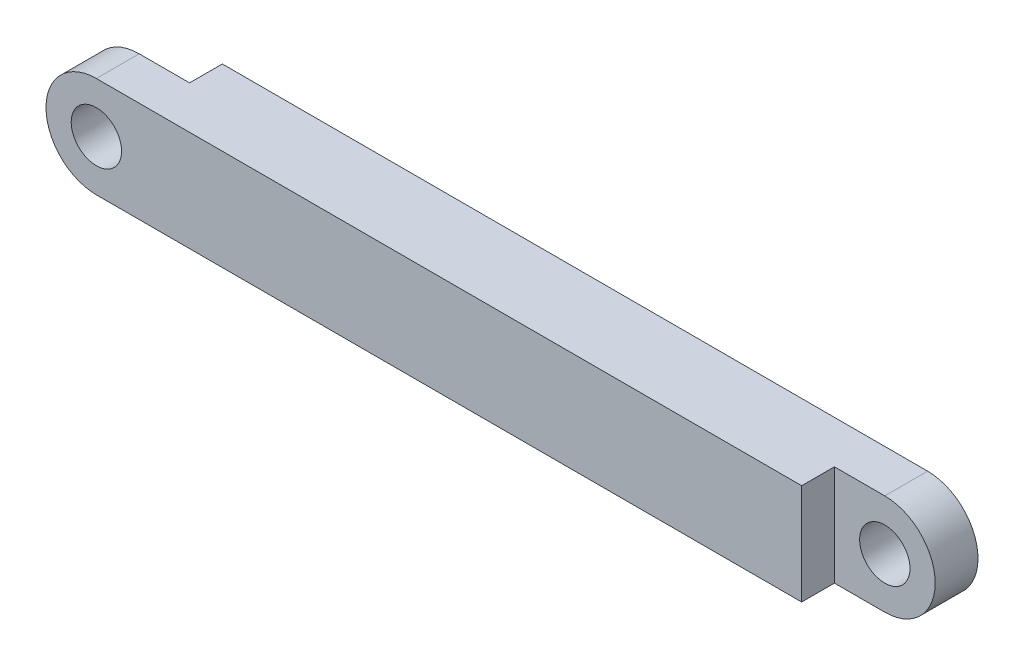
SolidWorks part; units mm, degrees
ref_plane "Спереди" through (0, 0, 0) normal (0, 0, 1) x (1, 0, 0)
ref_plane "Сверху" through (0, 0, 0) normal (0, 1, 0) x (1, 0, 0)
ref_plane "Справа" through (0, 0, 0) normal (1, 0, 0) x (0, 0, -1)
sketch "Эскиз1" plane through (0, 0, 0) normal (0, 0, 1) x (1, 0, 0)
  line L0 (-17.3575, -5.4234) -> (36.8251, 20.3496) construction
  line L1 (-2715.2651, -523.2425) -> (-2635.2651, -523.2425) construction
  line L2 (-40.1408, -46.1699) -> (39.8592, -46.1699) construction
  line L6 (0, 0) -> (-300, 0) construction
  line L7 (0, 20) -> (-300, 20)
  line L8 (0, -20) -> (-300, -20)
  line L12 (0, 0) -> (-50000, 0) construction
  circle A6 centre (-300, 0) radius 10
  circle A7 centre (0, 0) radius 10
  arc A8 (-300, -20) -> (-300, 20) centre (-300, 0) cw
  arc A10 (0, 20) -> (0, -20) centre (0, 0) cw
  dimension "D4" = 20
  dimension "D5" = 20
  dimension "D3" = 20
  dimension "D1" = 300
  dimension "D2" = 80
extrude "Бобышка-Вытянуть1" add sketch "Эскиз1" along normal mid plane 30
sketch "Эскиз2" plane through (0, 0, 15) normal (0, 0, 1) x (1, 0, 0)
  line L0 (-20, -20) -> (-20, 20)
  line L1 (-20, -20) -> (20, -20)
  line L2 (-20, 20) -> (20, 20)
  line L3 (20, -20) -> (20, 20)
  line L4 (0, 20) -> (0, -20) construction
  line L5 (-20, 0) -> (20, 0) construction
  line L6 (0, 20) -> (-300, 20) construction
  arc A0 (0, -20) -> (0, 20) centre (0, 0) ccw construction
  point P1 (0, 0)
  point P3 (0, 0)
  point P4 (0, 0)
  point P5 (0, 0)
  point P6 (0, 0)
  point P7 (0, 0)
  point P10 (0, 0)
  point P12 (0, 0)
  point P17 (0, 0)
  point P19 (0, 0)
extrude "Вырез-Вытянуть2" cut sketch "Эскиз2" against normal blind 13
sketch "Эскиз3" plane through (0, 0, -15) normal (0, 0, -1) x (-1, 0, 0)
  line L0 (0, 20) -> (300, 20) construction
  line L1 (320, -20) -> (280, -20)
  line L2 (320, -20) -> (320, 20)
  line L3 (320, 20) -> (280, 20)
  line L4 (280, -20) -> (280, 20)
  line L5 (320, -20) -> (280, 20) construction
  line L6 (320, 20) -> (280, -20) construction
  circle A0 centre (300, 0) radius 10 construction
  circle A1 centre (300, 0) radius 10 construction
  arc A2 (300, -20) -> (300, 20) centre (300, 0) ccw construction
extrude "Вырез-Вытянуть3" cut sketch "Эскиз3" against normal blind 13
